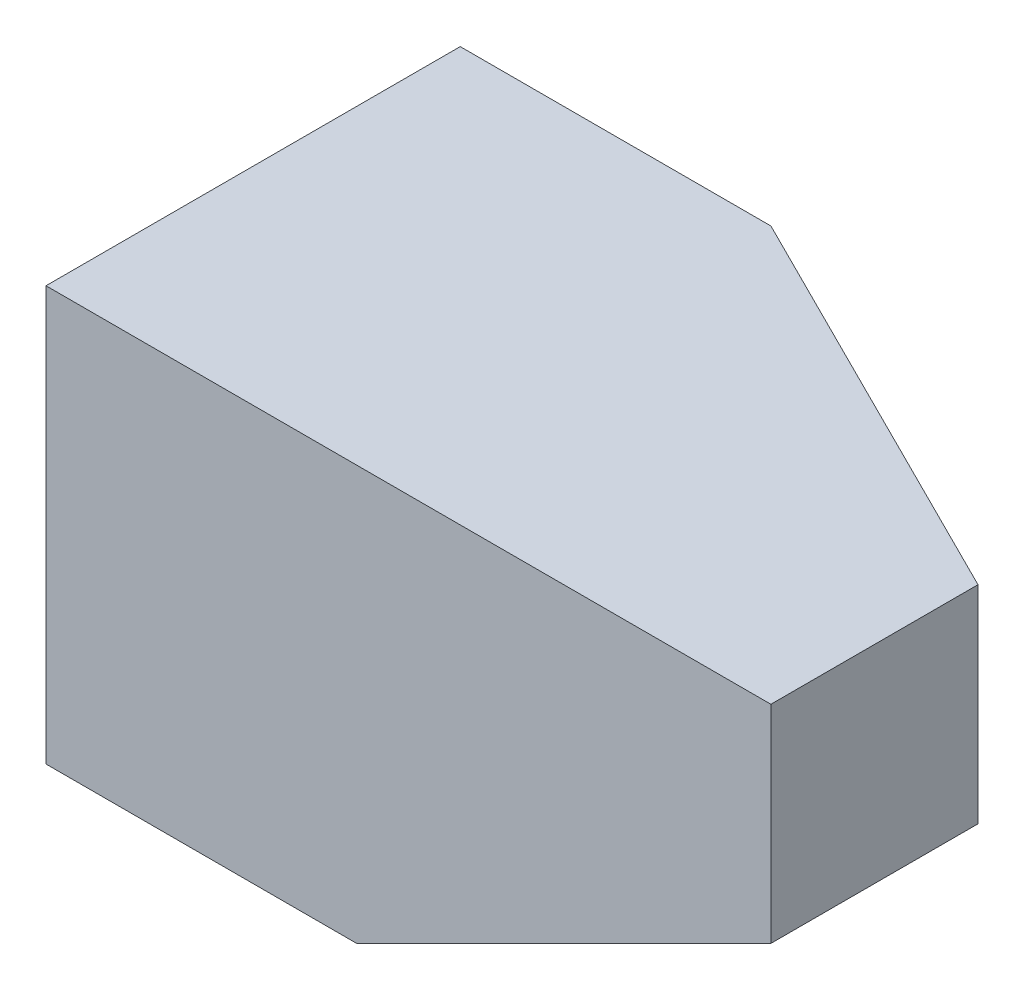
SolidWorks part; units mm, degrees
ref_plane "前基準面" through (0, 0, 0) normal (0, 0, 1) x (1, 0, 0)
ref_plane "上基準面" through (0, 0, 0) normal (0, 1, 0) x (1, 0, 0)
ref_plane "右基準面" through (0, 0, 0) normal (1, 0, 0) x (0, 0, -1)
sketch "草圖1" plane through (0, 0, 0) normal (0, 1, 0) x (1, 0, 0)
  line L1 (-30, -20) -> (40, -20)
  line L2 (-30, -20) -> (-30, 20)
  line L3 (-30, 20) -> (40, 20)
  line L4 (40, -20) -> (40, 20)
  point P4 (37.5397, 16.0714)
  dimension "D1" = 20
  dimension "D2" = 30
  dimension "D3" = 40
  dimension "D4" = 40
extrude "填料-伸長1" add sketch "草圖1" along normal blind 40 contours L3 L4 L1 L2
sketch "草圖2" plane through (0, 0, 0) normal (0, -1, 0) x (1, 0, 0)
  line L0 (40, 0) -> (0, -20)
  line L1 (40, 20) -> (40, -20) construction
  line L2 (-30, -20) -> (40, -20) construction
  line L3 (0, -20) -> (40, -20)
  line L4 (40, -20) -> (40, 0)
  dimension "D1" = 40
extrude "除料-伸長1" cut sketch "草圖2" against normal through all
sketch "草圖3" plane through (0, 0, 0) normal (0, 0, 1) x (1, 0, 0)
  line L0 (0, 40) -> (0, 0) construction
  line L1 (40, 0) -> (0, 0)
  line L2 (40, 0) -> (40, 20)
  line L3 (40, 20) -> (0, 20)
  line L4 (0, 0) -> (0, 20)
extrude "除料-伸長2" cut sketch "草圖3" against normal blind 20
sketch "草圖4" plane through (0, 0, 0) normal (0, 0, -1) x (-1, 0, 0)
  line L0 (0, 0) -> (-40, 20)
  line L1 (-40, 20) -> (-40, 0)
  line L2 (-40, 0) -> (0, 0)
extrude "除料-伸長3" cut sketch "草圖4" against normal blind 20
sketch "草圖5" plane through (0, 0, 0) normal (1, 0, 0) x (0, 0, -1)
  line L0 (0, 0) -> (20, 20)
  line L1 (20, 20) -> (20, 0)
  line L2 (20, 0) -> (0, 0)
extrude "除料-伸長4" cut sketch "草圖5" against normal through all
